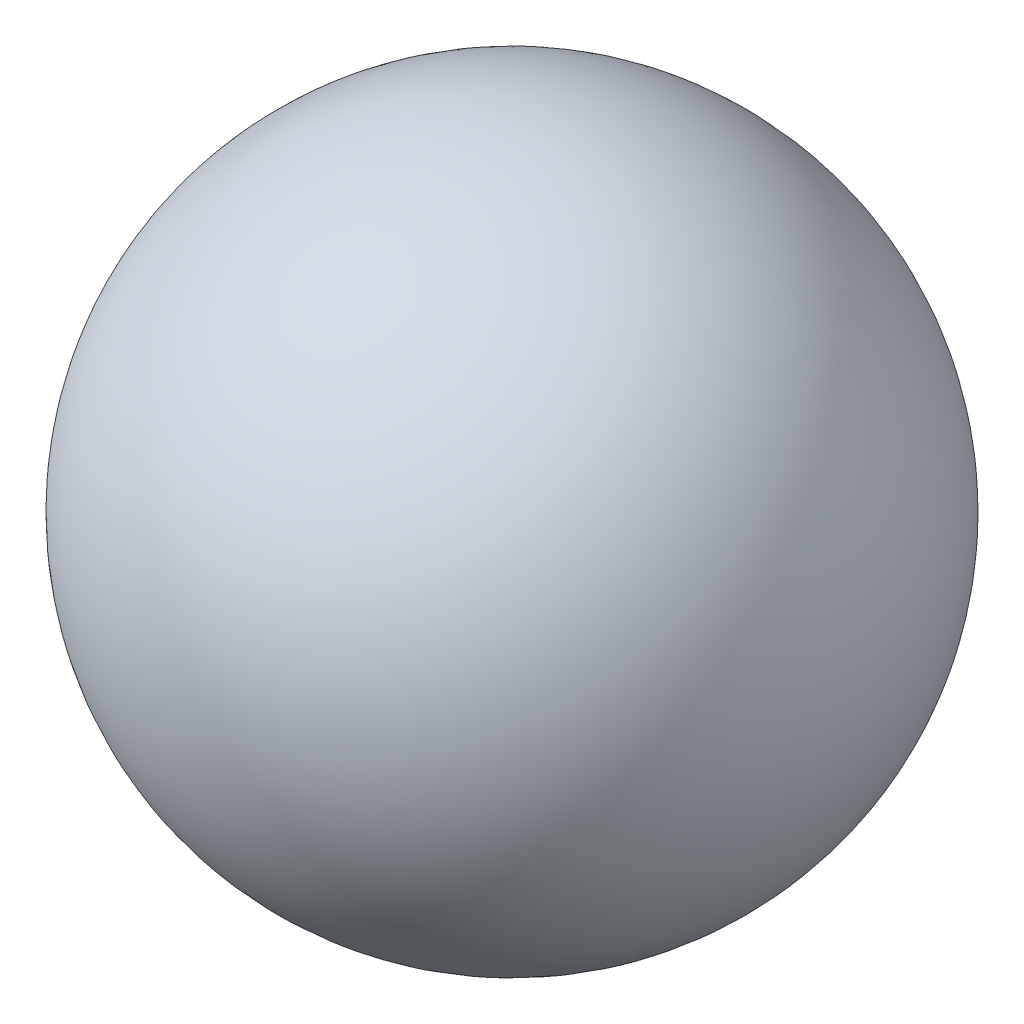
SolidWorks part; units mm, degrees
ref_plane "Plane1" through (0, 0, 0) normal (0, 0, 1) x (1, 0, 0)
ref_plane "Plane2" through (0, 0, 0) normal (0, 1, 0) x (1, 0, 0)
ref_plane "Plane3" through (0, 0, 0) normal (1, 0, 0) x (0, 0, -1)
sketch "Эскиз3" plane through (0, 0, 0) normal (0, 0, 1) x (1, 0, 0)
  line L0 (-2000, 0) -> (2000, 0) construction
  line L1 (-600, 0) -> (600, 0)
  ellipse E0 centre (0, 0) end of major axis (0, -600) minor radius 600 (600, 0) -> (-600, 0) ccw
revolve "Основание-Повернуть" add sketch "Эскиз3" angle 360 about L0
